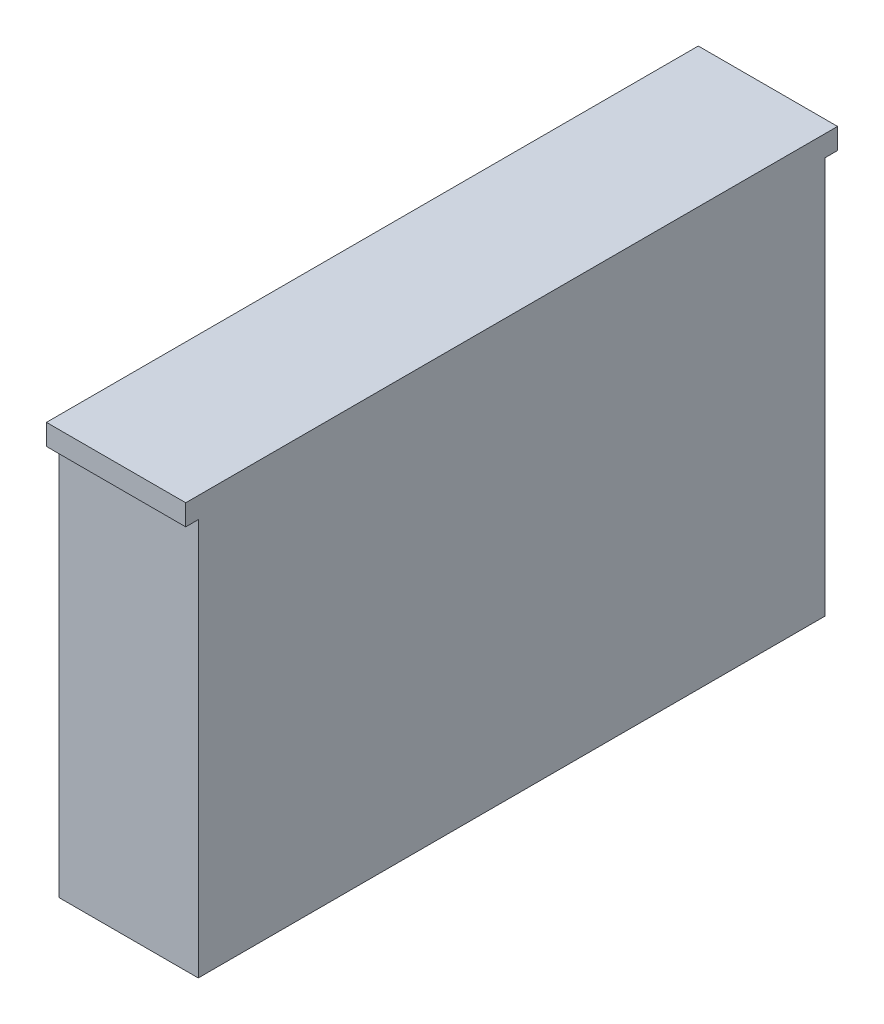
SolidWorks part; units mm, degrees
ref_plane "Alzado" through (0, 0, 0) normal (0, 0, 1) x (1, 0, 0)
ref_plane "Planta" through (0, 0, 0) normal (0, 1, 0) x (1, 0, 0)
ref_plane "Vista lateral" through (0, 0, 0) normal (1, 0, 0) x (0, 0, -1)
sketch "Croquis2" plane through (0, 0, 0) normal (1, 0, 0) x (0, 0, -1)
  line L1 (225, -150) -> (-225, -150)
  line L2 (225, -150) -> (225, 150)
  line L3 (225, 150) -> (-225, 150)
  line L4 (-225, -150) -> (-225, 150)
  line L5 (225, -150) -> (-225, 150) construction
  line L6 (225, 150) -> (-225, -150) construction
  point P0 (0, 0)
  dimension "D1" = 300
  dimension "D2" = 450
extrude "Saliente-Extruir1" add sketch "Croquis2" along normal blind 100
sketch "Croquis3" plane through (0, 0, 0) normal (-1, 0, 0) x (0, 0, 1)
  line L0 (-85.1737, 98.5116) -> (-2.5894, 8.4513) construction
  line L1 (-822.5697, 83.8671) -> (1.4303, 83.8671) construction
sketch "Croquis4" plane through (0, 0, -225) normal (0, 0, -1) x (-1, 0, 0)
  line L0 (-100, 150) -> (0, 150) construction
  line L5 (-100, 150) -> (0, 150)
  line L6 (0, 150) -> (0, 135)
  line L7 (0, -150) -> (0, 150) construction
  line L8 (0, 135) -> (-100, 135)
  line L9 (-100, -150) -> (-100, 150) construction
  line L10 (-100, 135) -> (-100, 150)
  point P0 (-79.3167, 150)
  dimension "D1" = 15
extrude "Saliente-Extruir2" add sketch "Croquis4" along normal blind 9
sketch "Croquis5" plane through (0, 0, 225) normal (0, 0, 1) x (1, 0, 0)
  line L1 (0, 150) -> (100, 150)
  line L2 (100, 150) -> (100, 135)
  line L3 (100, 135) -> (0, 135)
  line L4 (0, 135) -> (0, 150)
extrude "Saliente-Extruir3" add sketch "Croquis5" along normal blind 9
sketch "Croquis6" plane through (0, 0, -225) normal (0, 0, -1) x (-1, 0, 0)
  line L0 (-45.7416, -114.9273) -> (182.2584, -114.9273) construction
sketch "Croquis7" plane through (0, 0, -225) normal (0, 0, -1) x (-1, 0, 0)
  line L0 (-17.8265, -149.264) -> (210.1735, -149.264) construction
  line L1 (-208.937, -73.3363) -> (-75.6037, -73.3363) construction
sketch "Croquis8" plane through (0, -150, 0) normal (0, -1, 0) x (1, 0, 0)
  line L0 (-86.3236, 82.273) -> (47.0097, 82.273) construction
sketch "Croquis9" plane through (0, 0, -225) normal (0, 0, -1) x (-1, 0, 0)
  line L0 (-15.6165, -222.2282) -> (212.3835, -222.2282) construction
sketch "Croquis10" plane through (0, 0, 225) normal (0, 0, 1) x (1, 0, 0)
  line L0 (83.941, -64.3158) -> (311.941, -64.3158) construction
  line L1 (87.7954, -141.2246) -> (315.7954, -141.2246) construction
  line L2 (88.2849, -170.1548) -> (316.2849, -170.1548) construction
